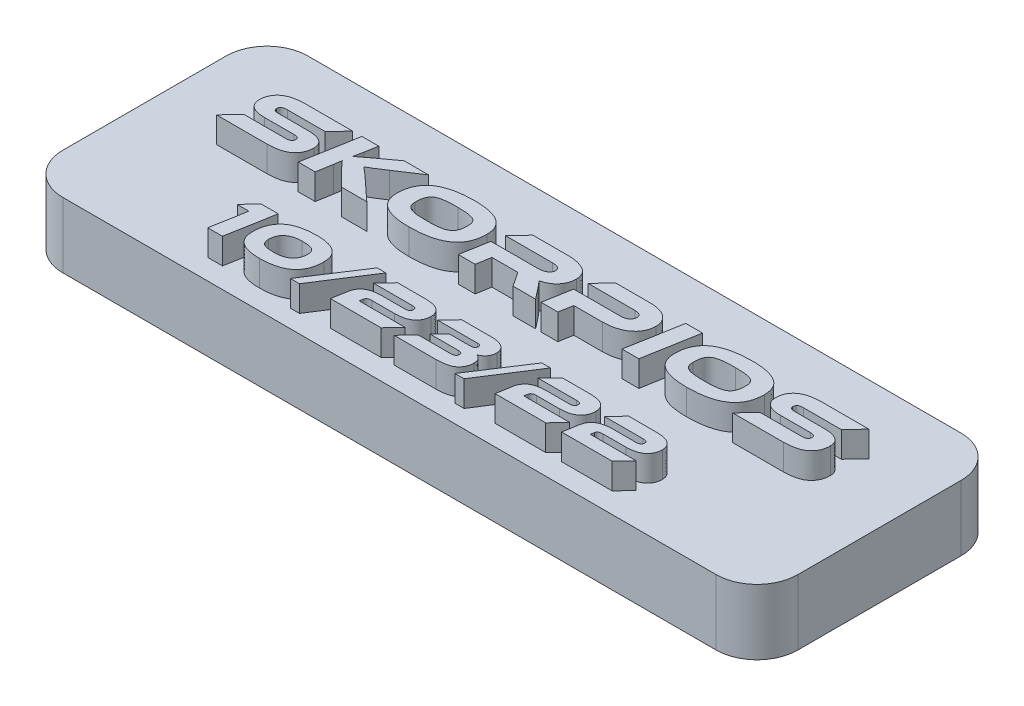
SolidWorks part; units mm, degrees
ref_plane "Front Plane" through (0, 0, 0) normal (0, 0, 1) x (1, 0, 0)
ref_plane "Top Plane" through (0, 0, 0) normal (0, 1, 0) x (1, 0, 0)
ref_plane "Right Plane" through (0, 0, 0) normal (1, 0, 0) x (0, 0, -1)
sketch "Sketch1" plane through (0, 0, 0) normal (0, 1, 0) x (1, 0, 0)
  line L1 (-28.575, 9.525) -> (28.575, 9.525)
  line L2 (-28.575, 9.525) -> (-28.575, -9.525)
  line L3 (-28.575, -9.525) -> (28.575, -9.525)
  line L4 (28.575, 9.525) -> (28.575, -9.525)
  line L5 (-28.575, 9.525) -> (28.575, -9.525) construction
  line L6 (-28.575, -9.525) -> (28.575, 9.525) construction
  point P0 (0, 0)
  dimension "D1" = 57.15
  dimension "D2" = 19.05
extrude "Boss-Extrude1" add sketch "Sketch1" along normal up to surface (5.08 mm away)
fillet "Fillet1" radius 3.175 4 edges at (-28.575, 2.54, 9.525) (-28.575, 2.54, -9.525) (28.575, 2.54, 9.525) (28.575, 2.54, -9.525)
sketch "Sketch3" plane through (0, 5.08, 0) normal (0, 1, 0) x (1, 0, 0)
  line L0 (28.575, -7.9375) -> (-28.575, -7.9375) construction
  line L1 (28.575, -6.35) -> (28.575, 6.35) construction
  line L2 (-28.575, 6.35) -> (-28.575, -6.35) construction
  line L3 (28.575, 0) -> (-28.575, 0) construction
  line L5 (-25.4, -9.525) -> (25.4, -9.525) construction
  line L6 (25.4, 9.525) -> (-25.4, 9.525) construction
  text T0 "Skorpios" font "Ethnocentric Rg" height in points 16
  text T1 "10/23/22\r\n" font "Ethnocentric Rg" height in points 14
  point P8 (-28.575, 0)
  dimension "D1" = 1.5875
extrude "Boss-Extrude2" add sketch "Sketch3" along normal blind 2
sketch "Sketch4" plane through (0, 0, 0) normal (0, -1, 0) x (1, 0, 0)
  line L0 (25.4, 0) -> (-25.4, 0) construction
  circle A0 centre (-25.4, 0) radius 0.9
  circle A1 centre (25.4, 0) radius 0.9
  point P3 (0, 0)
  dimension "D2" = 1.8
  dimension "D1" = 50.8
extrude "Cut-Extrude1" cut sketch "Sketch4" against normal blind 4
